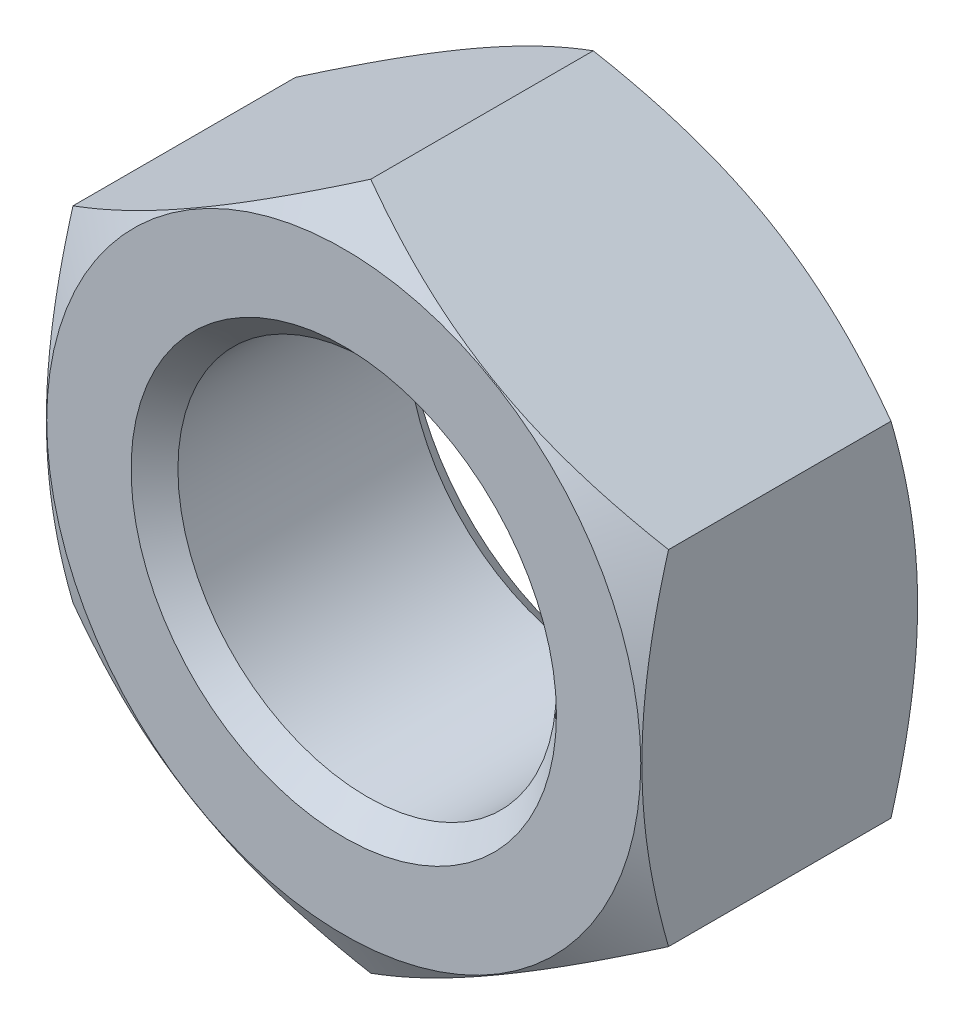
SolidWorks part; units mm, degrees
material "AISI 304"
ref_plane "Спереди" through (0, 0, 0) normal (0, 0, 1) x (1, 0, 0)
ref_plane "Сверху" through (0, 0, 0) normal (0, 1, 0) x (1, 0, 0)
ref_plane "Справа" through (0, 0, 0) normal (1, 0, 0) x (0, 0, -1)
sketch "Эскиз1" plane through (0, 0, 0) normal (0, 0, 1) x (1, 0, 0)
  line L1 (0, 16.1658) -> (-14, 8.0829)
  line L2 (-14, 8.0829) -> (-14, -8.0829)
  line L3 (-14, -8.0829) -> (0, -16.1658)
  line L4 (0, -16.1658) -> (14, -8.0829)
  line L5 (14, -8.0829) -> (14, 8.0829)
  line L6 (14, 8.0829) -> (0, 16.1658)
  circle A0 centre (0, 0) radius 16.1658 construction
  circle A1 centre (0, 0) radius 8.8985
  dimension "D1" = 17.797
  dimension "D2" = 28
extrude "Бобышка-Вытянуть1" add sketch "Эскиз1" against normal blind 13
cosmetic thread "Условное изображение резьбы1" parameters "D2"=20
sketch "Эскиз2" plane through (0, 0, 0) normal (1, 0, 0) x (0, 0, -1)
  line L0 (0, 0) -> (-50000, 0) construction
  line L1 (0, 13.9658) -> (5.7735, 23.9658)
  line L2 (0, 8.0829) -> (0, 16.1658) construction
  line L3 (5.7735, 23.9658) -> (0, 23.9658)
  line L4 (0, 23.9658) -> (0, 13.9658)
  line L5 (13, 16.1658) -> (0, 16.1658) construction
  line L6 (6.5, 16.1658) -> (6.5, -49983.8342) construction
  line L7 (13, 23.9658) -> (13, 13.9658)
  line L8 (7.2265, 23.9658) -> (13, 23.9658)
  line L9 (13, 13.9658) -> (7.2265, 23.9658)
  point P12 (6.5, 16.1658)
  dimension "D1" = 10
  dimension "D2" = 30
  dimension "D3" = 16.1658
  dimension "D4" = 2.2
revolve "Вырез-Повернуть1" cut sketch "Эскиз2" angle 360 about L0
chamfer "Фаска1" distance 1.1015 angle 45 2 edges at (8.8985, 0, -13) (8.8985, 0, 0)
